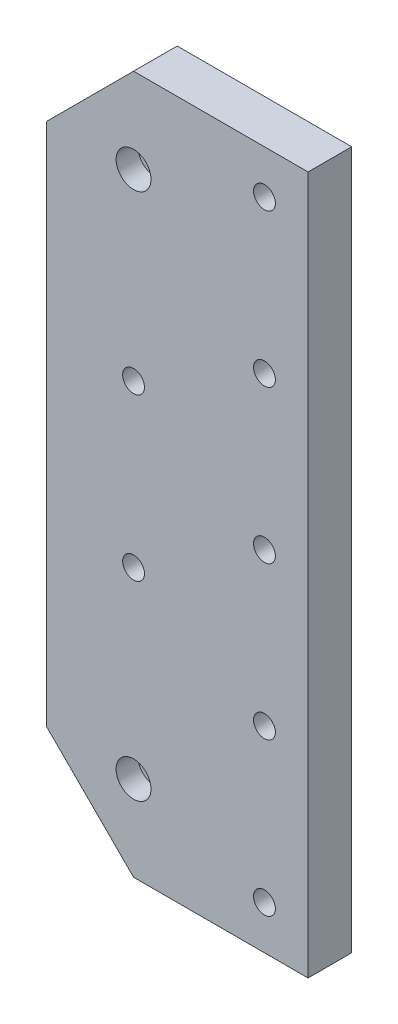
SolidWorks part; units mm, degrees
ref_plane "Plano frontal" through (0, 0, 0) normal (0, 0, 1) x (1, 0, 0)
ref_plane "Plano superior" through (0, 0, 0) normal (0, 1, 0) x (1, 0, 0)
ref_plane "Plano direito" through (0, 0, 0) normal (1, 0, 0) x (0, 0, -1)
other "Gráfico1"
other "Gráfico (Fechado) -1"
sketch "Esboço1" plane through (0, 0, 0) normal (0, 0, 1) x (1, 0, 0)
  line L0 (0.06, 112.5601) -> (0.06, -47.4399)
  line L1 (0.06, -47.4399) -> (-39.94, -47.4399)
  line L2 (-59.94, -27.4399) -> (-39.94, -47.4399)
  line L3 (-59.94, -27.4399) -> (-59.94, 92.5601)
  line L4 (-59.94, 92.5601) -> (-39.94, 112.5601)
  line L5 (-39.94, 112.5601) -> (0.06, 112.5601)
  line L6 (-39.94, 14.0601) -> (-39.94, 11.5601)
  line L7 (-42.9949, 32.5601) -> (-30.9185, 32.5601)
  line L8 (-39.94, -23.9399) -> (-39.94, -27.9399)
  circle A0 centre (-9.94, 102.5601) radius 2.5
  circle A1 centre (-9.94, 67.5601) radius 2.5
  circle A2 centre (-9.94, 32.5601) radius 2.5
  circle A3 centre (-39.94, 51.0601) radius 2.5
  circle A4 centre (-39.94, 14.0601) radius 2.5
  circle A5 centre (-9.94, -2.4399) radius 2.5
  circle A6 centre (-9.94, -37.4399) radius 2.5
  circle A7 centre (-39.94, -27.9399) radius 4
  circle A8 centre (-39.94, 93.0601) radius 4
  dimension "D3" = 42
extrude "Ressalto-extrusão1" add sketch "Esboço1" along normal blind 10
sketch "Esboço2" plane through (0, 0, 0) normal (0, 0, -1) x (-1, 0, 0)
  circle A0 centre (39.94, 93.0601) radius 4
  circle A1 centre (39.94, -27.9399) radius 4
extrude "Ressalto-extrusão2" add sketch "Esboço2" against normal blind 5
